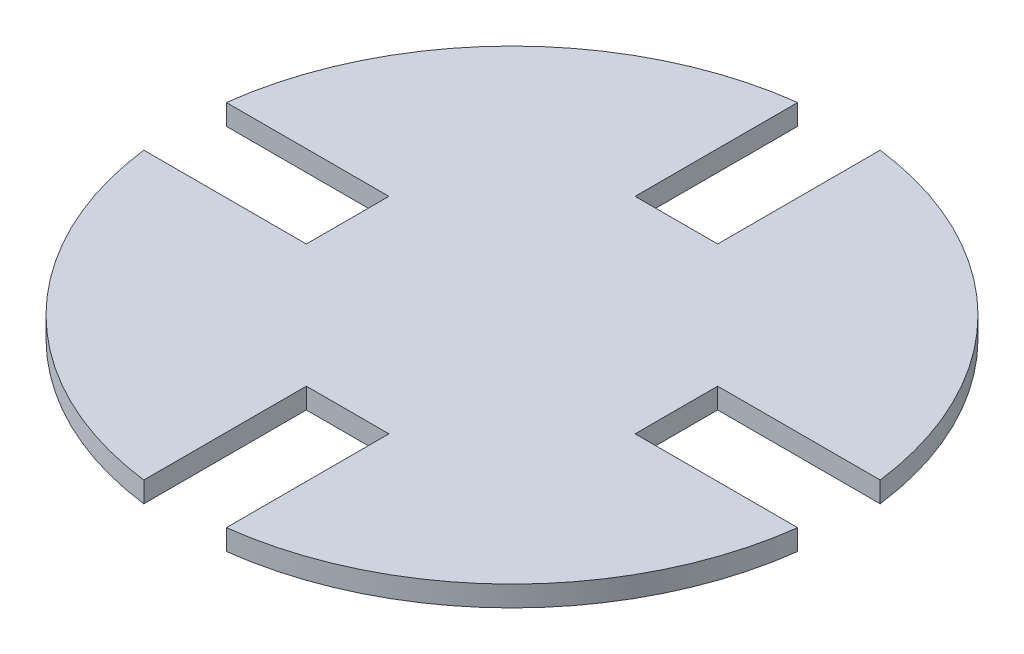
SolidWorks part; units mm, degrees
ref_plane "Front Plane" through (0, 0, 0) normal (0, 0, 1) x (1, 0, 0)
ref_plane "Top Plane" through (0, 0, 0) normal (0, 1, 0) x (1, 0, 0)
ref_plane "Right Plane" through (0, 0, 0) normal (1, 0, 0) x (0, 0, -1)
sketch "Sketch1" plane through (0, 0, 0) normal (0, 1, 0) x (1, 0, 0)
  circle A0 centre (0, 0) radius 101.3746
extrude "Boss-Extrude1" add sketch "Sketch1" along normal blind 6.35
sketch "Sketch2" plane through (0, 6.35, 0) normal (0, 1, 0) x (1, 0, 0)
  line L0 (-12.7, -50.5746) -> (12.7, -50.5746)
  line L1 (-12.7, -101.3746) -> (12.7, -101.3746)
  line L2 (-12.7, 101.3746) -> (-12.7, 57.0789)
  line L3 (-12.7, 101.3746) -> (12.7, 101.3746)
  line L4 (12.7, 101.3746) -> (12.7, 50.5746)
  line L5 (12.7, -50.5746) -> (12.7, -101.3746)
  line L6 (-12.7, -50.5746) -> (-12.7, -101.3746)
  line L7 (-12.7, 50.5746) -> (12.7, 50.5746)
  line L8 (0, 0) -> (0, 101.3746) construction
  line L9 (0, 0) -> (0, -101.3746) construction
  line L10 (-12.7, 57.0789) -> (-12.7, 50.5746)
  line L11 (50.5746, 12.7) -> (50.5746, -12.7)
  line L12 (101.3746, -12.7) -> (50.5746, -12.7)
  line L13 (57.0789, 12.7) -> (50.5746, 12.7)
  line L14 (101.3746, 12.7) -> (57.0789, 12.7)
  line L15 (101.3746, 12.7) -> (101.3746, -12.7)
  line L16 (12.7, -50.5746) -> (-12.7, -50.5746)
  line L17 (-12.7, -101.3746) -> (-12.7, -50.5746)
  line L18 (12.7, -57.0789) -> (12.7, -50.5746)
  line L19 (12.7, -101.3746) -> (12.7, -57.0789)
  line L20 (12.7, -101.3746) -> (-12.7, -101.3746)
  line L21 (-50.5746, -12.7) -> (-50.5746, 12.7)
  line L22 (-101.3746, 12.7) -> (-50.5746, 12.7)
  line L23 (-57.0789, -12.7) -> (-50.5746, -12.7)
  line L24 (-101.3746, -12.7) -> (-57.0789, -12.7)
  line L25 (-101.3746, -12.7) -> (-101.3746, 12.7)
  circle A0 centre (0, 0) radius 101.3746 construction
  point P0 (0, 0)
  point P15 (0, 50.5746)
  point P17 (0, -50.5746)
  point P19 (0, 101.3746)
  point P20 (0, -101.3746)
  point P38 (0, 0)
  circle M10 centre (0, 0) radius 101.3746
  dimension "D1" = 50.8
  dimension "D2" = 25.4
  dimension "D3" = 25.4
  dimension "D4" = 50.8
  dimension "D5" = 4
extrude "Cut-Extrude1" cut sketch "Sketch2" against normal through all contours L24 L23 L21 L22 M10 | L2 L10 L7 L4 M10 | L14 L13 L11 L12 M10 | L0 L6 L5 M10
